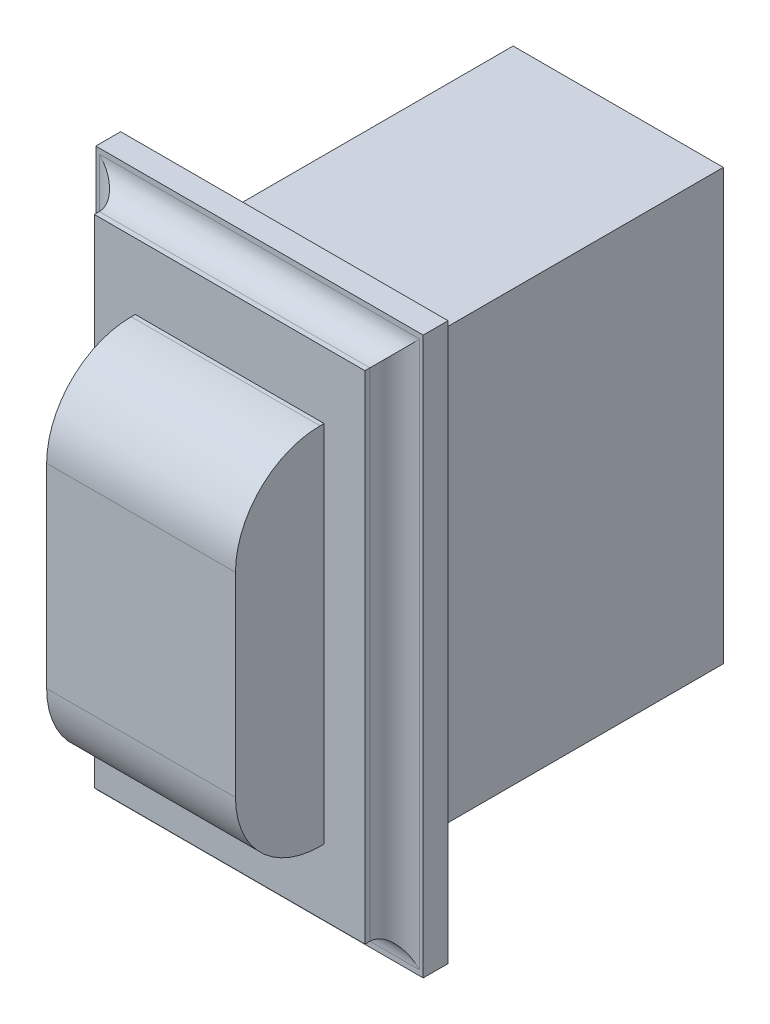
SolidWorks part; units mm, degrees
ref_plane "Front Plane" through (0, 0, 0) normal (0, 0, 1) x (1, 0, 0)
ref_plane "Top Plane" through (0, 0, 0) normal (0, 1, 0) x (1, 0, 0)
ref_plane "Right Plane" through (0, 0, 0) normal (1, 0, 0) x (0, 0, -1)
sketch "Sketch1" plane through (0, 0, 0) normal (0, 0, 1) x (1, 0, 0)
  line L1 (-16.7132, 28.4226) -> (16.7132, 28.4226)
  line L2 (-16.7132, 28.4226) -> (-16.7132, -28.4226)
  line L3 (-16.7132, -28.4226) -> (16.7132, -28.4226)
  line L4 (16.7132, 28.4226) -> (16.7132, -28.4226)
  line L5 (-16.7132, 28.4226) -> (16.7132, -28.4226) construction
  line L6 (-16.7132, -28.4226) -> (16.7132, 28.4226) construction
  point P0 (0, 0)
  dimension "D1" = 33.4264
  dimension "D2" = 56.8452
extrude "Boss-Extrude1" add sketch "Sketch1" along normal blind 2.54
sketch "Sketch2" plane through (0, 0, 2.54) normal (0, 0, 1) x (1, 0, 0)
  line L1 (-13.8176, 25.3492) -> (13.8176, 25.3492)
  line L2 (-13.8176, 25.3492) -> (-13.8176, -25.3492)
  line L3 (-13.8176, -25.3492) -> (13.8176, -25.3492)
  line L4 (13.8176, 25.3492) -> (13.8176, -25.3492)
  line L5 (-13.8176, 25.3492) -> (13.8176, -25.3492) construction
  line L6 (-13.8176, -25.3492) -> (13.8176, 25.3492) construction
  point P0 (0, 0)
  dimension "D1" = 27.6352
  dimension "D2" = 50.6984
extrude "Boss-Extrude2" add sketch "Sketch2" along normal blind 3.048
sketch "Sketch3" plane through (0, 0, 5.588) normal (0, 0, 1) x (1, 0, 0)
  line L1 (-9.6393, 18.5928) -> (9.6393, 18.5928)
  line L2 (-9.6393, 18.5928) -> (-9.6393, -18.5928)
  line L3 (-9.6393, -18.5928) -> (9.6393, -18.5928)
  line L4 (9.6393, 18.5928) -> (9.6393, -18.5928)
  line L5 (-9.6393, 18.5928) -> (9.6393, -18.5928) construction
  line L6 (-9.6393, -18.5928) -> (9.6393, 18.5928) construction
  point P0 (0, 0)
  dimension "D1" = 37.1856
  dimension "D2" = 19.2786
extrude "Boss-Extrude3" add sketch "Sketch3" along normal blind 9.0424
fillet "Fillet1" radius 2.54 4 edges at (0, 25.3492, 2.54) (-13.8176, 0, 2.54) (0, -25.3492, 2.54) (13.8176, 0, 2.54)
fillet "Fillet7" radius 8.636 2 edges at (0, -18.5928, 14.6304) (0, 18.5928, 14.6304)
sketch "Sketch4" plane through (0, 0, 0) normal (0, 0, -1) x (-1, 0, 0)
  line L1 (-10.7315, -21.9456) -> (10.7315, -21.9456)
  line L2 (-10.7315, -21.9456) -> (-10.7315, 21.9456)
  line L3 (-10.7315, 21.9456) -> (10.7315, 21.9456)
  line L4 (10.7315, -21.9456) -> (10.7315, 21.9456)
  line L5 (-10.7315, -21.9456) -> (10.7315, 21.9456) construction
  line L6 (-10.7315, 21.9456) -> (10.7315, -21.9456) construction
  point P0 (0, 0)
  dimension "D1" = 21.463
  dimension "D2" = 43.8912
extrude "Boss-Extrude4" add sketch "Sketch4" along normal blind 34.0868
